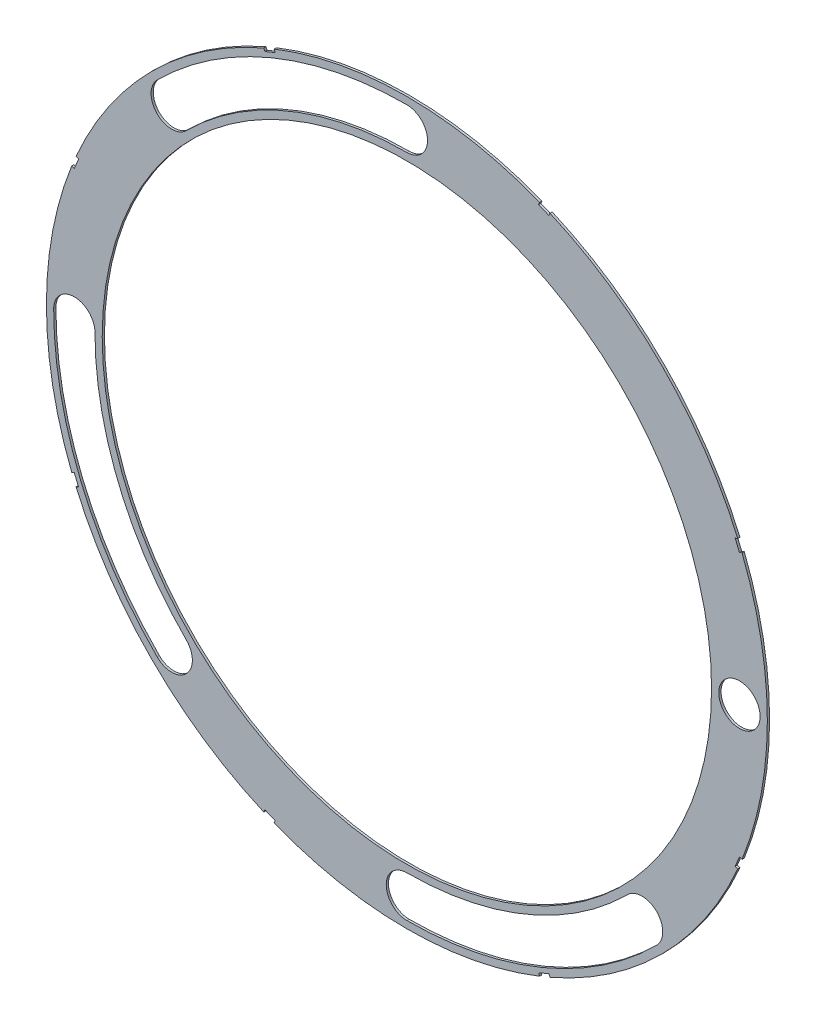
SolidWorks part; units mm, degrees
material "PTFE (general)"
ref_plane "Front Plane" through (0, 0, 0) normal (0, 0, 1) x (1, 0, 0)
ref_plane "Top Plane" through (0, 0, 0) normal (0, 1, 0) x (1, 0, 0)
ref_plane "Right Plane" through (0, 0, 0) normal (1, 0, 0) x (0, 0, -1)
sketch "Sketch4" plane through (0, 0, 0) normal (0, 0, 1) x (1, 0, 0)
  circle A0 centre (0, 0) radius 82.042
  dimension "D1" = 164.084
extrude "Boss-Extrude2" add sketch "Sketch4" along normal blind 0.508
sketch "Sketch5" plane through (0, 0, 0.508) normal (0, 0, 1) x (1, 0, 0)
  circle A0 centre (0, 0) radius 69.342
  circle A1 centre (0, 0) radius 82.042 construction
  dimension "D1" = 12.7
extrude "Cut-Extrude5" cut sketch "Sketch5" against normal through all
sketch "Sketch6" plane through (0, 0, 0.508) normal (0, 0, 1) x (1, 0, 0)
  line L0 (0, 0) -> (75.692, 0) construction
  line L1 (0, 0) -> (58.0125, -58.0125) construction
  line L2 (0, 0) -> (0, -82.042) construction
  line L3 (0, 0) -> (0, -82.042) construction
  line L4 (0, 0) -> (58.0125, -58.0125) construction
  line L5 (0, 0) -> (-58.0125, -58.0125) construction
  line L6 (0, 0) -> (-58.0125, -58.0125) construction
  line L7 (0, 0) -> (-82.042, 0) construction
  line L8 (0, 0) -> (-82.042, 0) construction
  line L9 (0, 0) -> (-58.0125, 58.0125) construction
  line L10 (0, 0) -> (-58.0125, 58.0125) construction
  line L11 (0, 0) -> (0, 82.042) construction
  line L12 (0, 0) -> (0, 82.042) construction
  line L13 (0, 0) -> (50.1996, -50.1996) construction
  line L14 (0, 0) -> (-50.1996, -50.1996) construction
  circle A0 centre (75.692, 0) radius 4.699
  circle A1 centre (0, 0) radius 82.042 construction
  arc A2 (56.845, -56.845) -> (50.1996, -50.1996) centre (53.5223, -53.5223) ccw
  arc A3 (50.1996, -50.1996) -> (0, -70.993) centre (0, 0) cw
  arc A4 (0, -70.993) -> (0, -80.391) centre (0, -75.692) ccw
  arc A5 (0, -80.391) -> (56.845, -56.845) centre (0, 0) ccw
  arc A6 (-56.845, -56.845) -> (-50.1996, -50.1996) centre (-53.5223, -53.5223) ccw
  arc A7 (-50.1996, -50.1996) -> (-70.993, 0) centre (0, 0) cw
  arc A8 (-80.391, 0) -> (-56.845, -56.845) centre (0, 0) ccw
  arc A9 (-70.993, 0) -> (-80.391, 0) centre (-75.692, 0) ccw
  arc A10 (-56.845, 56.845) -> (-50.1996, 50.1996) centre (-53.5223, 53.5223) ccw
  arc A11 (-50.1996, 50.1996) -> (0, 70.993) centre (0, 0) cw
  arc A12 (0, 80.391) -> (-56.845, 56.845) centre (0, 0) ccw
  arc A13 (0, 70.993) -> (0, 80.391) centre (0, 75.692) ccw
  circle A16 centre (0, 0) radius 69.342 construction
  point P4 (53.5223, -53.5223)
  point P11 (0, -75.692)
  point P13 (-53.5223, -53.5223)
  point P27 (-75.692, 0)
  point P30 (0, 0)
  point P36 (-53.5223, 53.5223)
  point P41 (0, 75.692)
  dimension "D2" = 9.398
  dimension "D3" = 45
  dimension "D4" = 90
  dimension "D1" = 6.35
  dimension "D6" = 6.35
  dimension "D7" = 9.398
  dimension "D8" = 4.699
  dimension "D9" = 4.699
  dimension "D5" = 6.35
  dimension "D10" = 90
extrude "Cut-Extrude6" cut sketch "Sketch6" against normal through all
sketch "Sketch8" plane through (0, 0, 0.508) normal (0, 0, 1) x (1, 0, 0)
  line L0 (76.8696, 30.4658) -> (75.8976, 32.8124)
  line L1 (76.8696, 30.4658) -> (75.6963, 29.9798)
  line L2 (75.6963, 29.9798) -> (74.7243, 32.3264)
  line L3 (75.8976, 32.8124) -> (74.7243, 32.3264)
  line L4 (76.8696, 30.4658) -> (74.7243, 32.3264) construction
  line L5 (75.8976, 32.8124) -> (75.6963, 29.9798) construction
  line L6 (0, 0) -> (82.042, 0) construction
  line L7 (-30.4658, 76.8696) -> (-32.8124, 75.8976)
  line L8 (-30.4658, 76.8696) -> (-29.9798, 75.6963)
  line L9 (-32.8124, 75.8976) -> (-32.3264, 74.7243)
  line L10 (-29.9798, 75.6963) -> (-32.3264, 74.7243)
  line L11 (-32.8124, 75.8976) -> (-29.9798, 75.6963) construction
  line L12 (-30.4658, 76.8696) -> (-32.3264, 74.7243) construction
  line L13 (-75.8976, 32.8124) -> (-76.8696, 30.4658)
  line L14 (-75.8976, 32.8124) -> (-74.7243, 32.3264)
  line L15 (-74.7243, 32.3264) -> (-75.6963, 29.9798)
  line L16 (-76.8696, 30.4658) -> (-75.6963, 29.9798)
  line L17 (-75.8976, 32.8124) -> (-75.6963, 29.9798) construction
  line L18 (-76.8696, 30.4658) -> (-74.7243, 32.3264) construction
  line L19 (-76.8696, -30.4658) -> (-75.8976, -32.8124)
  line L20 (-76.8696, -30.4658) -> (-75.6963, -29.9798)
  line L21 (-75.6963, -29.9798) -> (-74.7243, -32.3264)
  line L22 (-75.8976, -32.8124) -> (-74.7243, -32.3264)
  line L23 (-76.8696, -30.4658) -> (-74.7243, -32.3264) construction
  line L24 (-75.8976, -32.8124) -> (-75.6963, -29.9798) construction
  line L25 (-32.8124, -75.8976) -> (-30.4658, -76.8696)
  line L26 (-32.8124, -75.8976) -> (-32.3264, -74.7243)
  line L27 (-32.3264, -74.7243) -> (-29.9798, -75.6963)
  line L28 (-30.4658, -76.8696) -> (-29.9798, -75.6963)
  line L29 (-32.8124, -75.8976) -> (-29.9798, -75.6963) construction
  line L30 (-30.4658, -76.8696) -> (-32.3264, -74.7243) construction
  line L31 (30.4658, -76.8696) -> (32.8124, -75.8976)
  line L32 (30.4658, -76.8696) -> (29.9798, -75.6963)
  line L33 (29.9798, -75.6963) -> (32.3264, -74.7243)
  line L34 (32.8124, -75.8976) -> (32.3264, -74.7243)
  line L35 (30.4658, -76.8696) -> (32.3264, -74.7243) construction
  line L36 (32.8124, -75.8976) -> (29.9798, -75.6963) construction
  line L37 (75.8976, -32.8124) -> (76.8696, -30.4658)
  line L38 (75.8976, -32.8124) -> (74.7243, -32.3264)
  line L39 (74.7243, -32.3264) -> (75.6963, -29.9798)
  line L40 (76.8696, -30.4658) -> (75.6963, -29.9798)
  line L41 (75.8976, -32.8124) -> (75.6963, -29.9798) construction
  line L42 (76.8696, -30.4658) -> (74.7243, -32.3264) construction
  line L43 (32.8124, 75.8976) -> (30.4658, 76.8696)
  line L44 (32.8124, 75.8976) -> (32.3264, 74.7243)
  line L45 (32.3264, 74.7243) -> (29.9798, 75.6963)
  line L46 (30.4658, 76.8696) -> (29.9798, 75.6963)
  line L47 (32.8124, 75.8976) -> (29.9798, 75.6963) construction
  line L48 (30.4658, 76.8696) -> (32.3264, 74.7243) construction
  circle A0 centre (0, 0) radius 82.042 construction
  point P3 (-31.3961, 75.7969)
  point P11 (-75.7969, 31.3961)
  point P14 (75.7969, 31.3961)
  point P20 (-75.7969, -31.3961)
  point P25 (-31.3961, -75.7969)
  point P26 (0, 0)
  point P31 (31.3961, -75.7969)
  point P36 (75.7969, -31.3961)
  point P44 (31.3961, 75.7969)
  point P46 (0, 0)
  dimension "D5" = 1.27
  dimension "D6" = 2.54
  dimension "D7" = 1.27
  dimension "D9" = 0.635
  dimension "D10" = 112.5
  dimension "D14" = 0.635
  dimension "D21" = 22.5
  dimension "D22" = 0.635
  dimension "D11" = 8
extrude "Cut-Extrude11" cut sketch "Sketch8" against normal through all
